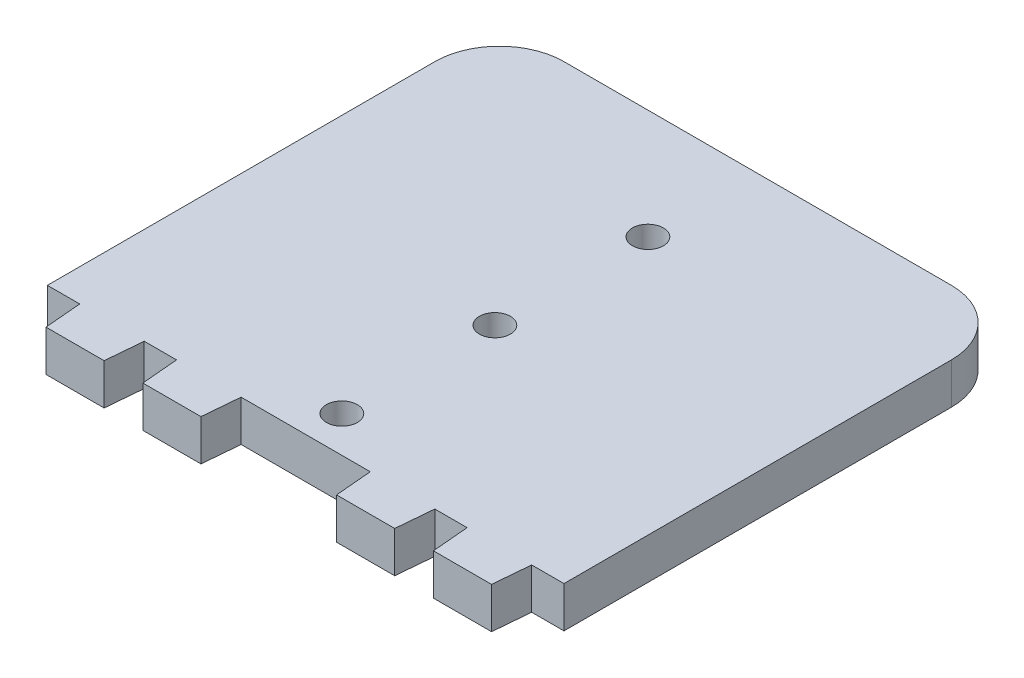
SolidWorks part; units mm, degrees
ref_plane "Front Plane" through (0, 0, 0) normal (0, 0, 1) x (1, 0, 0)
ref_plane "Top Plane" through (0, 0, 0) normal (0, 1, 0) x (1, 0, 0)
ref_plane "Right Plane" through (0, 0, 0) normal (1, 0, 0) x (0, 0, -1)
sketch "Sketch1" plane through (0, 0, 0) normal (0, 1, 0) x (1, 0, 0)
  line L0 (0, 0) -> (0, -38545.911) construction
  line L1 (-40, 35) -> (40, 35)
  line L2 (-40, 35) -> (-40, -35)
  line L3 (-40, -35) -> (40, -35)
  line L4 (40, 35) -> (40, -35)
  line L5 (-40, 35) -> (40, -35) construction
  line L6 (-40, -35) -> (40, 35) construction
  line L7 (-15, -35) -> (-15, -40.715) construction
  line L8 (-20, -35) -> (-10, -35)
  line L9 (-20, -35) -> (-19.5, -40.715)
  line L10 (-19.5, -40.715) -> (-10.5, -40.715)
  line L11 (-10, -35) -> (-10.5, -40.715)
  line L12 (15, -35) -> (15, -40.715) construction
  line L13 (10, -35) -> (10.5, -40.715)
  line L14 (19.5, -40.715) -> (10.5, -40.715)
  line L15 (20, -35) -> (19.5, -40.715)
  line L16 (20, -35) -> (10, -35)
  line L17 (-30, -1035.4841) -> (-30, 48964.5159) construction
  line L18 (-35, -35) -> (-25, -35)
  line L19 (-35, -35) -> (-34.5, -40.715)
  line L20 (-34.5, -40.715) -> (-25.5, -40.715)
  line L21 (-25, -35) -> (-25.5, -40.715)
  line L22 (-35, -35) -> (-34.5, -40.715)
  line L23 (-25, -35) -> (-25.5, -40.715)
  line L24 (-35, -35) -> (-34.5, -40.715)
  line L25 (-25, -35) -> (-25.5, -40.715)
  line L26 (-35, -35) -> (-34.5, -40.715)
  line L27 (-25, -35) -> (-25.5, -40.715)
  line L28 (-35, -35) -> (-34.5, -40.715)
  line L29 (-25, -35) -> (-25.5, -40.715)
  line L30 (-35, -35) -> (-34.5, -40.715)
  line L31 (-25, -35) -> (-25.5, -40.715)
  line L32 (-35, -35) -> (-34.5, -40.715)
  line L33 (-25, -35) -> (-25.5, -40.715)
  line L34 (-35, -35) -> (-34.5, -40.715)
  line L35 (-25, -35) -> (-25.5, -40.715)
  line L36 (25, -35) -> (25.5, -40.715)
  line L37 (35, -35) -> (34.5, -40.715)
  line L38 (25, -35) -> (25.5, -40.715)
  line L39 (35, -35) -> (34.5, -40.715)
  line L40 (25, -35) -> (25.5, -40.715)
  line L41 (35, -35) -> (34.5, -40.715)
  line L42 (25, -35) -> (25.5, -40.715)
  line L43 (35, -35) -> (34.5, -40.715)
  line L44 (25, -35) -> (25.5, -40.715)
  line L45 (35, -35) -> (34.5, -40.715)
  line L46 (25, -35) -> (25.5, -40.715)
  line L47 (35, -35) -> (34.5, -40.715)
  line L48 (25, -35) -> (25.5, -40.715)
  line L49 (35, -35) -> (34.5, -40.715)
  line L50 (25, -35) -> (25.5, -40.715)
  line L51 (34.5, -40.715) -> (25.5, -40.715)
  line L52 (35, -35) -> (34.5, -40.715)
  line L53 (35, -35) -> (25, -35)
  circle A0 centre (0, 18) radius 2.4
  circle A1 centre (0, -5.7) radius 2.4
  circle A2 centre (0, -29.4) radius 2.4
  point P0 (0, 0)
  point P13 (-15, -40.715)
  point P28 (-30, -35)
  point P30 (-30, -40.715)
  dimension "D14" = 4.8
  dimension "D16" = 4.8
  dimension "D17" = 4.8
  dimension "D1" = 10
  dimension "D2" = 9
  dimension "D3" = 5.715
  dimension "D4" = 0
  dimension "D6" = 70
  dimension "D5" = 15
  dimension "D8" = 10
  dimension "D9" = 9
  dimension "D10" = 5.715
  dimension "D11" = 15
  dimension "D12" = 80
  dimension "D13" = 23.7
  dimension "D7" = 29.3
  dimension "D15" = 23.7
extrude "Boss-Extrude1" add sketch "Sketch1" along normal blind 6.35 contours L15 L3 L13 L14 | L11 L3 L9 L10 | L4 L1 L2 L3 A0 | L21 L3 L19 L20 | L51 L37 L3 L36
fillet "Fillet1" radius 10 2 edges at (-40, 3.175, -35) (40, 3.175, -35)
equation "\"toothBaseWidth\"=0.01"
equation "\"toothEndWidth\"=0.009"
equation "\"toothLength\"= 0.005715"
equation "\"D2@Sketch1\"=\"toothEndWidth\""
equation "\"D1@Sketch1\"= \"toothBaseWidth\""
equation "\"D3@Sketch1\"=\"toothLength\""
equation "\"holeWidth\" = 0.009"
equation "\"motorHolderToothSeparation\" = 0.01"
equation "\"magnetHolderToothSeparation\" = 0.02"
equation "\"D10@Sketch1\"=\"toothLength\""
equation "\"D9@Sketch1\"=\"toothEndWidth\""
equation "\"D8@Sketch1\"=\"toothBaseWidth\""
